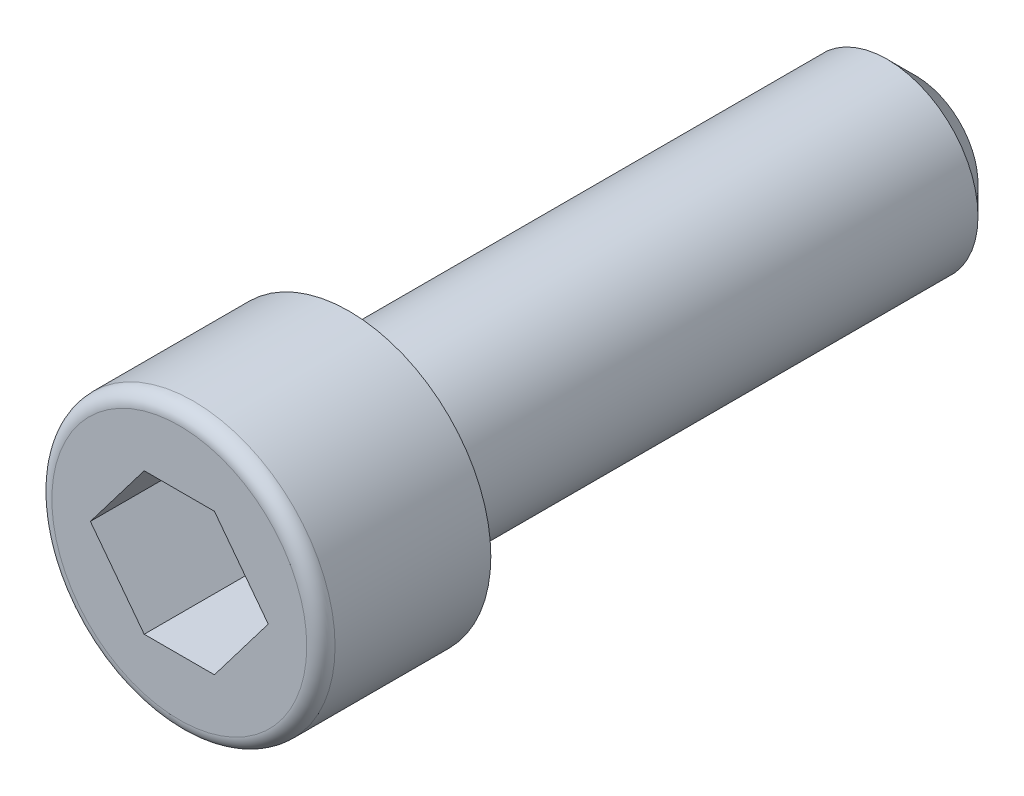
SolidWorks part; units mm, degrees
ref_plane "Plane1" through (0, 0, 0) normal (0, 0, 1) x (1, 0, 0)
ref_plane "Plane2" through (0, 0, 0) normal (0, 1, 0) x (1, 0, 0)
ref_plane "Plane3" through (0, 0, 0) normal (1, 0, 0) x (0, 0, -1)
sketch "Esquisse1" plane through (0, 0, 0) normal (0, 0, 1) x (1, 0, 0)
  circle A0 centre (0, 0) radius 5
  dimension "D1" = 10
extrude "Base-Extrusion" add sketch "Esquisse1" along normal blind 6
sketch "Esquisse2" plane through (0, 0, 0) normal (0, 0, -1) x (-1, 0, 0)
  circle A0 centre (0, 0) radius 3.2016
  circle A1 centre (0, 0) radius 5 construction
extrude "Boss.-Extru.1" add sketch "Esquisse2" along normal blind 20
sketch "Esquisse3" plane through (0, 0, 6) normal (0, 0, 1) x (1, 0, 0)
  line L0 (0, 0) -> (0, 4.2257) construction
  line L1 (0, 0) -> (4.4294, 0) construction
  line L2 (3.1401, 0) -> (1.2401, 2.5)
  line L3 (1.2401, 2.5) -> (-1.2401, 2.5)
  line L4 (-1.2401, 2.5) -> (-3.1401, 0)
  line L5 (-3.1401, 0) -> (-1.2401, -2.5)
  line L6 (-1.2401, -2.5) -> (1.2401, -2.5)
  line L7 (1.2401, -2.5) -> (3.1401, 0)
  dimension "D1" = 5
  dimension "D2" = 5
extrude "Enlèv. mat.-Extru.1" cut sketch "Esquisse3" against normal blind 5
fillet "Congé1" radius 0.5
chamfer "Chanfrein1" distance 1 angle 45
